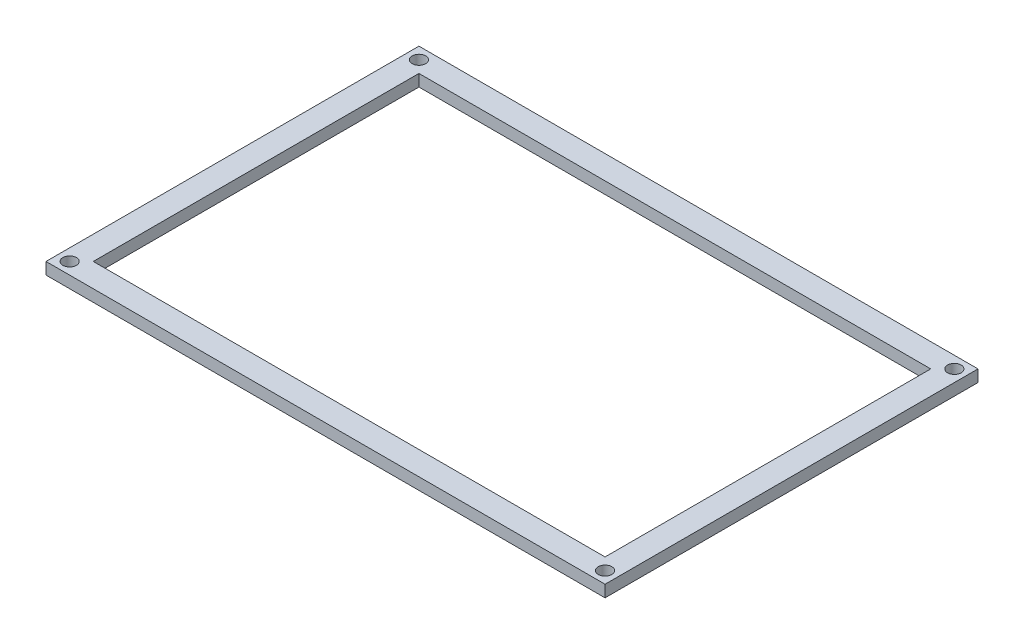
SolidWorks part; units mm, degrees
material "6061-T6 (SS)"
ref_plane "Front Plane" through (0, 0, 0) normal (0, 0, 1) x (1, 0, 0)
ref_plane "Top Plane" through (0, 0, 0) normal (0, 1, 0) x (1, 0, 0)
ref_plane "Right Plane" through (0, 0, 0) normal (1, 0, 0) x (0, 0, -1)
sketch "Sketch1" plane through (0, 0, 0) normal (0, 1, 0) x (1, 0, 0)
  line L0 (-60.08, 40.0801) -> (60.08, 40.0801)
  line L1 (-55, -35.0001) -> (55, -35.0001)
  line L2 (-55, -35.0001) -> (-55, 35.0001)
  line L3 (-55, 35.0001) -> (55, 35.0001)
  line L4 (55, -35.0001) -> (55, 35.0001)
  line L5 (-55, -35.0001) -> (55, 35.0001) construction
  line L6 (-55, 35.0001) -> (55, -35.0001) construction
  line L7 (60.08, -40.0801) -> (60.08, 40.0801)
  line L8 (-60.08, -40.0801) -> (60.08, -40.0801)
  line L9 (-60.08, -40.0801) -> (-60.08, 40.0801)
  point P0 (0, 0)
  dimension "D2" = 110
  dimension "D3" = 70.0001
  dimension "D1" = 5.08
extrude "Boss-Extrude1" add sketch "Sketch1" along normal blind 2.54 contours L9 L0 L7 L8
sketch "Sketch2" plane through (0, 2.54, 0) normal (0, 1, 0) x (1, 0, 0)
  line L0 (55, -35.0001) -> (60.08, -40.0801) construction
  line L1 (55, 0) -> (-55, 0) construction
  line L2 (55, -35.0001) -> (55, 35.0001) construction
  line L3 (-55, 35.0001) -> (-55, -35.0001) construction
  line L4 (0, -35.0001) -> (0, 35.0001) construction
  line L5 (-55, -35.0001) -> (55, -35.0001) construction
  line L6 (55, 35.0001) -> (-55, 35.0001) construction
  circle A0 centre (57.54, -37.5401) radius 1.4605
  circle A1 centre (57.54, 37.5401) radius 1.4605
  circle A2 centre (-57.54, 37.5401) radius 1.4605
  circle A3 centre (-57.54, -37.5401) radius 1.4605
  dimension "D1" = 2.921
extrude "Mounting Holes (4-40 Clearance)" cut sketch "Sketch2" against normal blind 2.54
equation "\"Length Needed for GPS\"=4.33071"
equation "\"D2@Sketch1\"=\"Length Needed for GPS\""
equation "\"Width Needed for GPS\"=2.75591"
equation "\"D3@Sketch1\"=\"Width Needed for GPS\""
